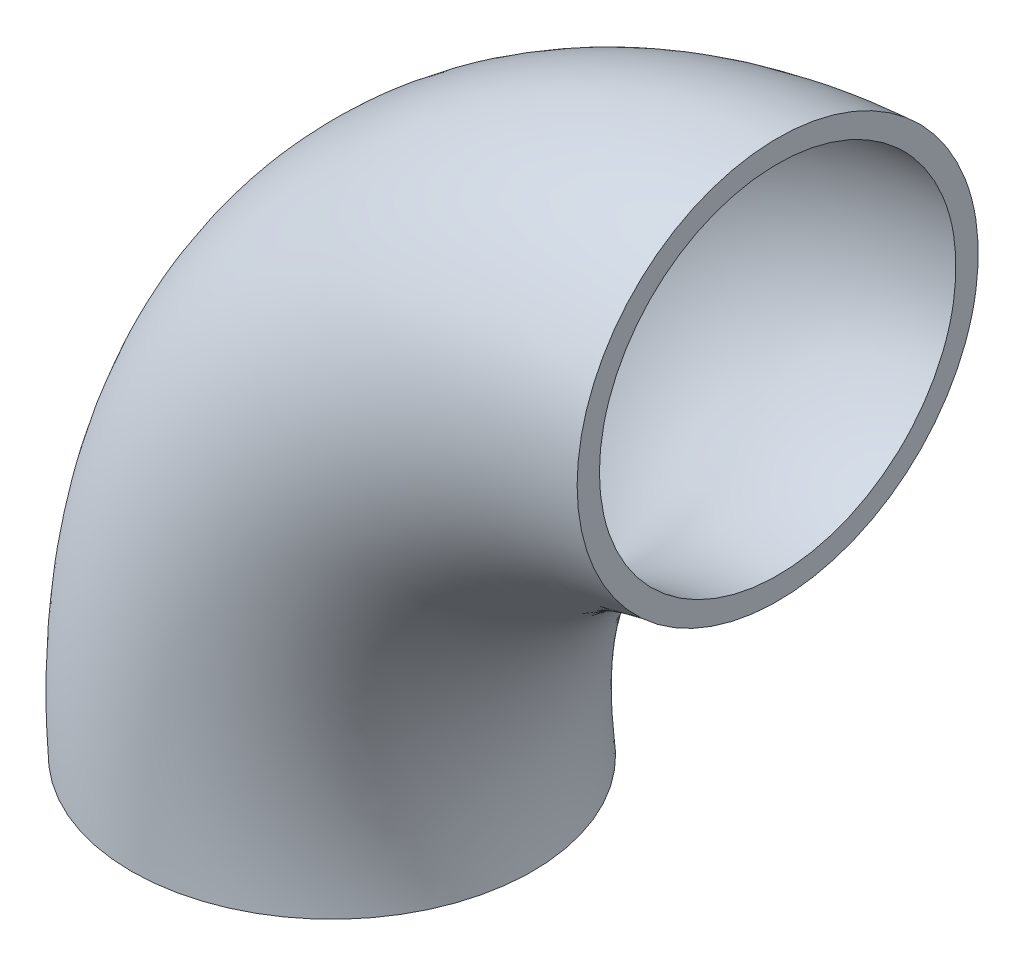
SolidWorks part; units mm, degrees
ref_plane "Alzado" through (0, 0, 0) normal (0, 0, 1) x (1, 0, 0)
ref_plane "Planta" through (0, 0, 0) normal (0, 1, 0) x (1, 0, 0)
ref_plane "Vista lateral" through (0, 0, 0) normal (1, 0, 0) x (0, 0, -1)
sketch "Croquis1" plane through (0, 0, 0) normal (0, 1, 0) x (1, 0, 0)
  circle A0 centre (0, 0) radius 16
  circle A1 centre (0, 0) radius 18
  dimension "D1" = 32
  dimension "D2" = 2
sketch "Croquis2" plane through (0, 0, 0) normal (0, 0, 1) x (1, 0, 0)
  line L0 (0, 0) -> (0, 50) construction
  line L1 (0, 50) -> (40, 50) construction
  arc A0 (0, 0) -> (40, 50) centre (45, 5) cw
  dimension "D1" = 50
  dimension "D2" = 40
sweep "Barrer1" add profiles "Croquis1" path "Croquis2"
